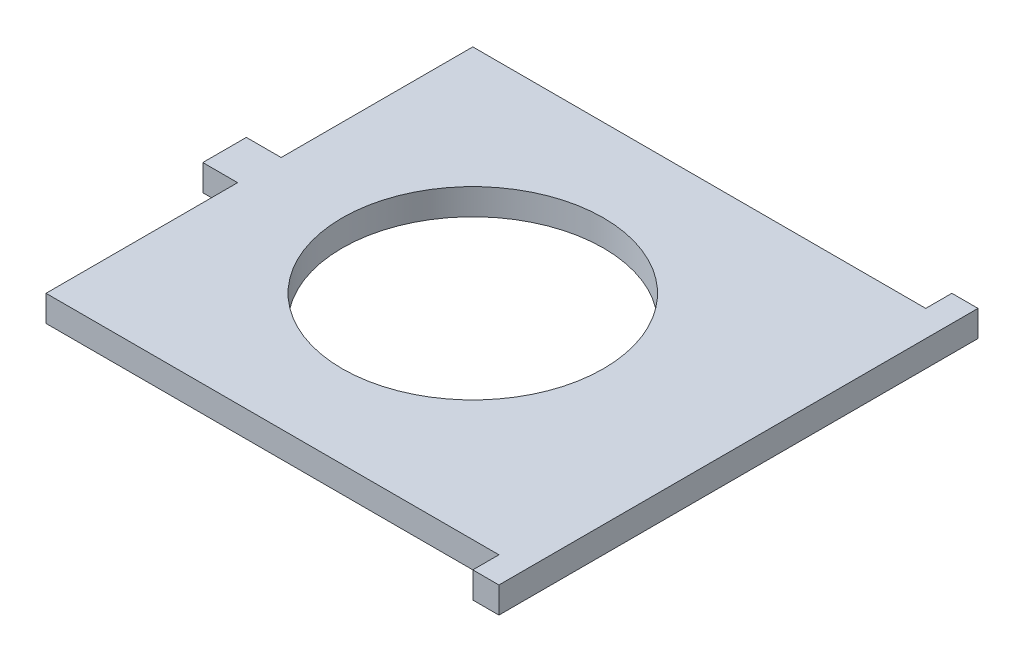
SolidWorks part; units mm, degrees
ref_plane "Front Plane" through (0, 0, 0) normal (0, 0, 1) x (1, 0, 0)
ref_plane "Top Plane" through (0, 0, 0) normal (0, 1, 0) x (1, 0, 0)
ref_plane "Right Plane" through (0, 0, 0) normal (1, 0, 0) x (0, 0, -1)
sketch "Sketch1" plane through (0, 0, 0) normal (0, 1, 0) x (1, 0, 0)
  line L0 (27.5, -24.5) -> (27.5, -27.5)
  line L1 (-24.5, -24.5) -> (24.5, -24.5)
  line L2 (-24.5, -24.5) -> (-24.5, 24.5)
  line L3 (-24.5, 24.5) -> (24.5, 24.5)
  line L4 (24.5, -24.5) -> (24.5, 24.5)
  line L5 (-24.5, -24.5) -> (24.5, 24.5) construction
  line L6 (-24.5, 24.5) -> (24.5, -24.5) construction
  line L7 (-24.5, -2.5) -> (-28.5, -2.5)
  line L8 (-24.5, -2.5) -> (-24.5, 2.5)
  line L9 (-24.5, 2.5) -> (-28.5, 2.5)
  line L10 (-28.5, -2.5) -> (-28.5, 2.5)
  line L11 (24.5, -24.5) -> (27.5, -24.5)
  line L12 (24.5, -24.5) -> (24.5, 24.5)
  line L13 (24.5, 24.5) -> (27.5, 24.5)
  line L14 (27.5, -24.5) -> (27.5, 24.5)
  line L15 (27.5, -27.5) -> (30.5, -27.5)
  line L16 (30.5, -27.5) -> (30.5, 27.5)
  line L17 (30.5, 27.5) -> (27.5, 27.5)
  line L18 (27.5, 27.5) -> (27.5, 24.5)
  line L19 (-28.5, 2.5) -> (-24.5, -2.5) construction
  line L20 (-28.5, -2.5) -> (-24.5, 2.5) construction
  circle A0 centre (0, 0) radius 15
  point P0 (0, 0)
  point P12 (-26.5, 0)
  dimension "D7" = 30
  dimension "D1" = 49
  dimension "D2" = 4
  dimension "D3" = 5
  dimension "D4" = 3
  dimension "D5" = 3
  dimension "D6" = 3
extrude "Boss-Extrude1" add sketch "Sketch1" along normal blind 3 contours L1 L4 L3 L2 A0 | L10 L7 L2 L9 | L11 L14 L13 L4 | L17 L18 L14 L0 L15 L16
